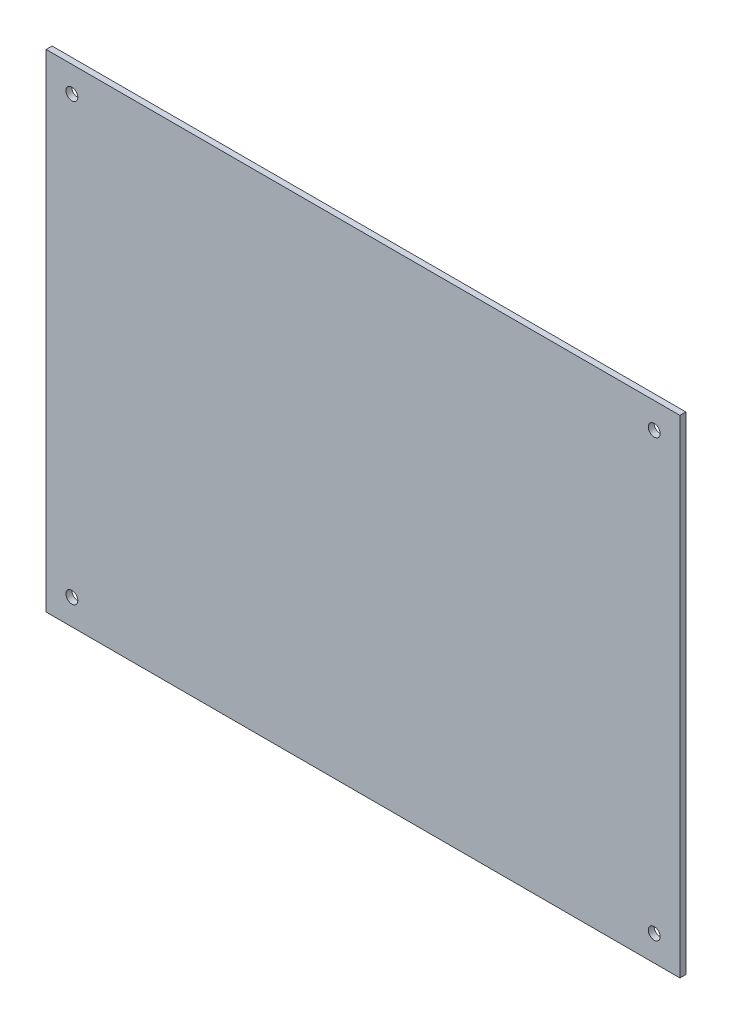
SolidWorks part; units mm, degrees
material "1060 合金"
ref_plane "前视基准面" through (0, 0, 0) normal (0, 0, 1) x (1, 0, 0)
ref_plane "上视基准面" through (0, 0, 0) normal (0, 1, 0) x (1, 0, 0)
ref_plane "右视基准面" through (0, 0, 0) normal (1, 0, 0) x (0, 0, -1)
sketch "草图1" plane through (0, 0, 0) normal (0, 0, 1) x (1, 0, 0)
  line L84 (352.6084, -1072.8029) -> (1952.6084, -1072.8029)
  line L85 (352.6084, -1072.8029) -> (352.6084, -2302.8029)
  line L86 (352.6084, -2302.8029) -> (1952.6084, -2302.8029)
  line L87 (1952.6084, -1072.8029) -> (1952.6084, -2302.8029)
  circle A108 centre (417.6084, -1137.8029) radius 15
  circle A109 centre (1887.6084, -1137.8029) radius 15
  circle A110 centre (1887.6084, -2237.8029) radius 15
  circle A111 centre (417.6084, -2237.8029) radius 15
  dimension "D25" = 1600
  dimension "D90" = 65
  dimension "D91" = 65
  dimension "D92" = 65
  dimension "D93" = 65
  dimension "D94" = 65
  dimension "D95" = 65
  dimension "D96" = 65
  dimension "D97" = 65
  dimension "D48" = 1230
extrude "凸台-拉伸1" add sketch "草图1" along normal blind 3
scale "缩放比例1" bodies to scale 101 104 102 103 108 scale about centroid uniform scaling no x scale factor 0.1 y scale factor 0.1 z scale factor 0.5
